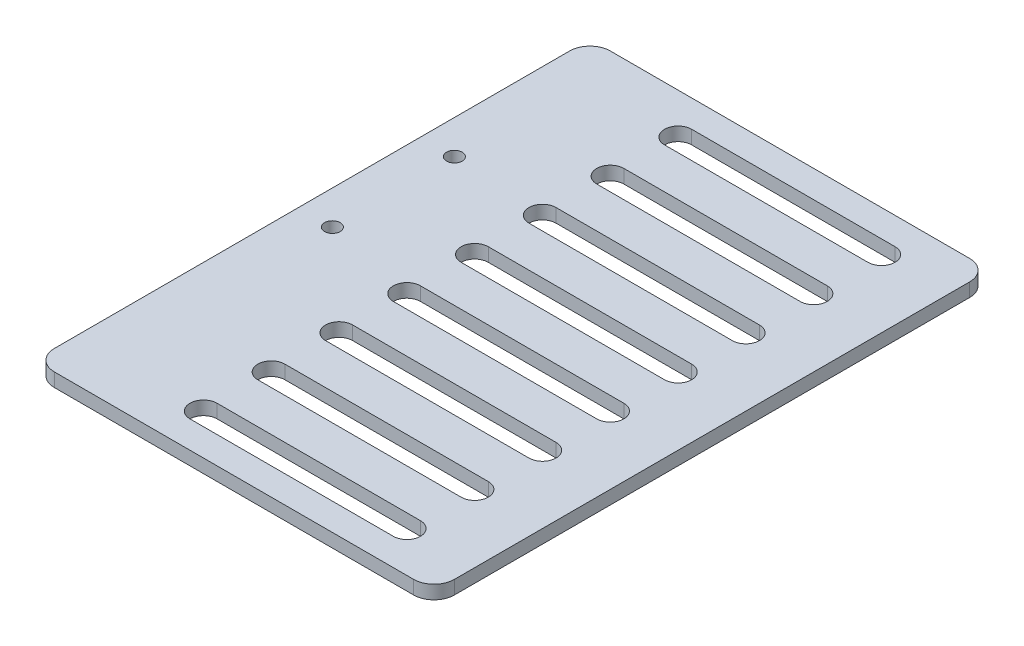
SolidWorks part; units mm, degrees
material "A-玻璃纤维"
ref_plane "Front" through (0, 0, 0) normal (0, 0, 1) x (1, 0, 0)
ref_plane "Top" through (0, 0, 0) normal (0, 1, 0) x (1, 0, 0)
ref_plane "Right" through (0, 0, 0) normal (1, 0, 0) x (0, 0, -1)
sketch "草图1" plane through (0, 0, 0) normal (0, 1, 0) x (1, 0, 0)
  line L0 (0, 0) -> (0, 18) construction
  line L1 (0, 2) -> (34.5, 2) construction
  line L2 (0, 0) -> (42.0463, 0) construction
  line L3 (64, -39) -> (5, -39)
  line L4 (64, -39) -> (64, 43)
  line L5 (64, 43) -> (5, 43)
  line L6 (5, -39) -> (5, 43) construction
  line L7 (64, -39) -> (5, 43) construction
  line L8 (64, 43) -> (5, -39) construction
  line L9 (5, 21) -> (-4, 21)
  line L10 (-4, 21) -> (-4, -3)
  line L11 (-4, -3) -> (5, -3)
  line L12 (5, -39) -> (5, -3)
  line L13 (5, 43) -> (5, 21)
  circle A0 centre (0, 0) radius 1.15
  circle A1 centre (0, 18) radius 1.15
  dimension "D2" = 2.3
  dimension "D6" = 5
  dimension "D1" = 18
  dimension "D3" = 59
  dimension "D4" = 82
  dimension "D5" = 2
  dimension "D7" = 3
  dimension "D8" = 3
  dimension "D9" = 4
extrude "凸台-拉伸1" add sketch "草图1" along normal blind 2
fillet "圆角1" radius 3 8 edges at (5, 1, -43) (64, 1, -43) (64, 1, 39) (5, 1, 39) (-4, 1, 3) (-4, 1, -21) (5, 1, 3) (5, 1, -21)
sketch "草图2" plane through (0, 2, 0) normal (0, 1, 0) x (1, 0, 0)
  line L0 (0, 18) -> (10, 18) construction
  line L1 (10, 18) -> (10, 0) construction
  line L2 (10, 0) -> (0, 0) construction
  line L3 (5, 40) -> (5, 24) construction
  circle A0 centre (10, 18) radius 1.15
  circle A1 centre (10, 0) radius 1.15
  dimension "D1" = 2.3
  dimension "D2" = 5
extrude "切除-拉伸1" cut sketch "草图2" against normal blind 2
sketch "草图3" plane through (0, 2, 0) normal (0, 1, 0) x (1, 0, 0)
  line L0 (5, 24) -> (5, -6)
  line L1 (5, -6) -> (-4, -6)
  line L2 (-4, -6) -> (-4, 24)
  line L3 (-4, 24) -> (5, 24)
  line L4 (-4, 18) -> (-4, 0) construction
  arc A0 (2, 21) -> (5, 24) centre (2, 24) ccw construction
extrude "切除-拉伸2" cut sketch "草图3" against normal blind 2
sketch "草图4" plane through (0, 2, 0) normal (0, 1, 0) x (1, 0, 0)
  line L0 (24, 37) -> (54, 37) construction
  line L10 (24, 39) -> (54, 39)
  line L11 (24, 35) -> (54, 35)
  line L12 (64, -36) -> (64, 40) construction
  line L13 (24, 27) -> (54, 27) construction
  line L14 (24, 29) -> (54, 29)
  line L15 (24, 25) -> (54, 25)
  line L16 (24, 17) -> (54, 17) construction
  line L17 (24, 19) -> (54, 19)
  line L18 (24, 15) -> (54, 15)
  line L19 (24, 7) -> (54, 7) construction
  line L20 (24, 9) -> (54, 9)
  line L21 (24, 5) -> (54, 5)
  line L22 (24, -3) -> (54, -3) construction
  line L23 (24, -1) -> (54, -1)
  line L24 (24, -5) -> (54, -5)
  line L25 (24, -13) -> (54, -13) construction
  line L26 (24, -11) -> (54, -11)
  line L27 (24, -15) -> (54, -15)
  line L28 (24, -23) -> (54, -23) construction
  line L29 (24, -21) -> (54, -21)
  line L30 (24, -25) -> (54, -25)
  line L31 (24, -33) -> (54, -33) construction
  line L32 (24, -31) -> (54, -31)
  line L33 (24, -35) -> (54, -35)
  line L34 (61, 43) -> (8, 43) construction
  arc A0 (24, 39) -> (24, 35) centre (24, 37) ccw
  arc A1 (54, 35) -> (54, 39) centre (54, 37) ccw
  arc A2 (24, 29) -> (24, 25) centre (24, 27) ccw
  arc A3 (54, 25) -> (54, 29) centre (54, 27) ccw
  arc A4 (24, 19) -> (24, 15) centre (24, 17) ccw
  arc A5 (54, 15) -> (54, 19) centre (54, 17) ccw
  arc A6 (24, 9) -> (24, 5) centre (24, 7) ccw
  arc A7 (54, 5) -> (54, 9) centre (54, 7) ccw
  arc A8 (24, -1) -> (24, -5) centre (24, -3) ccw
  arc A9 (54, -5) -> (54, -1) centre (54, -3) ccw
  arc A10 (24, -11) -> (24, -15) centre (24, -13) ccw
  arc A11 (54, -15) -> (54, -11) centre (54, -13) ccw
  arc A12 (24, -21) -> (24, -25) centre (24, -23) ccw
  arc A13 (54, -25) -> (54, -21) centre (54, -23) ccw
  arc A14 (24, -31) -> (24, -35) centre (24, -33) ccw
  arc A15 (54, -35) -> (54, -31) centre (54, -33) ccw
  point P2 (39, 37)
  point P12 (39, 27)
  point P19 (39, 17)
  point P26 (39, 7)
  point P33 (39, -3)
  point P40 (39, -13)
  point P47 (39, -23)
  point P54 (39, -33)
  dimension "D2" = 30
  dimension "D1" = 2
  dimension "D3" = 25
  dimension "D5" = 6
  dimension "D6" = 10
  dimension "D4" = 8
extrude "切除-拉伸3" cut sketch "草图4" against normal through all
